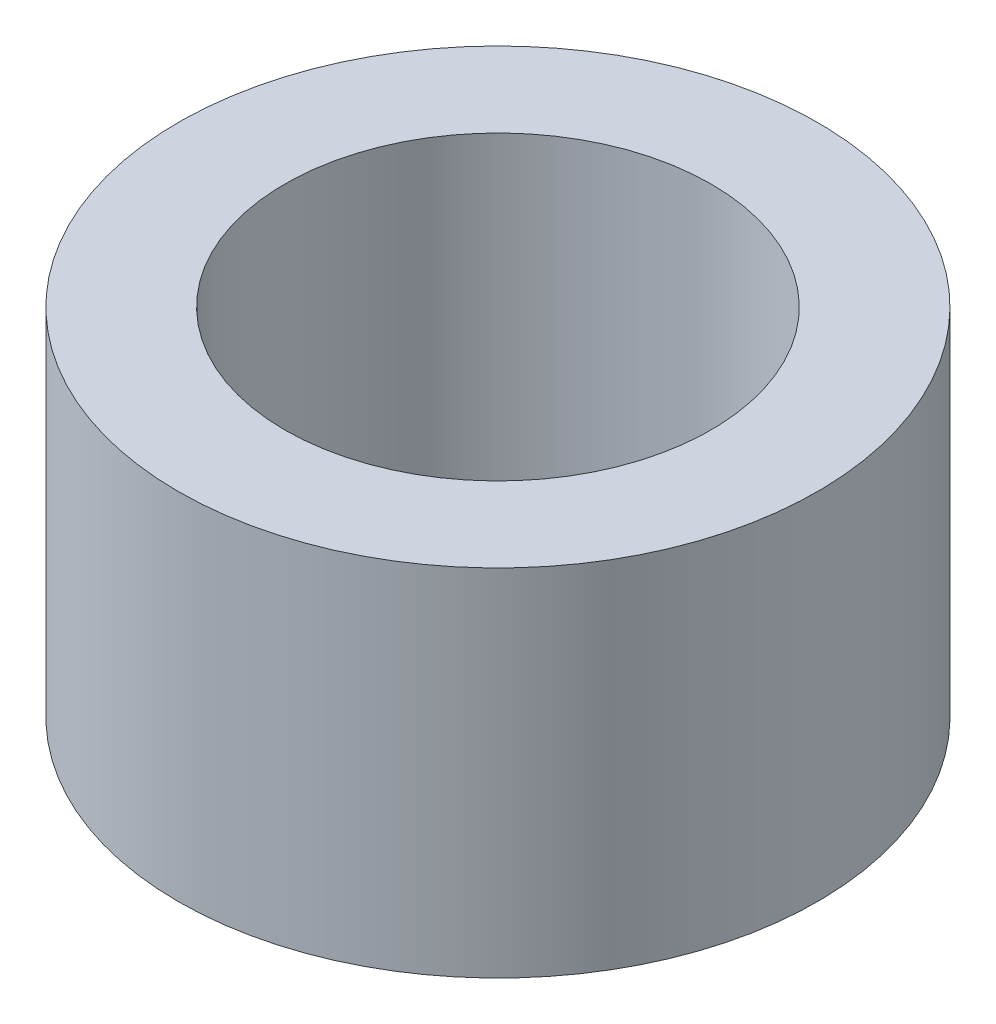
SolidWorks part; units mm, degrees
ref_plane "Front Plane" through (0, 0, 0) normal (0, 0, 1) x (1, 0, 0)
ref_plane "Top Plane" through (0, 0, 0) normal (0, 1, 0) x (1, 0, 0)
ref_plane "Right Plane" through (0, 0, 0) normal (1, 0, 0) x (0, 0, -1)
sketch "Sketch1" plane through (0, 0, 0) normal (0, 1, 0) x (1, 0, 0)
  circle A0 centre (0, 0) radius 9
extrude "Boss-Extrude1" add sketch "Sketch1" along normal blind 10
sketch "Sketch2" plane through (0, 10, 0) normal (0, 1, 0) x (1, 0, 0)
  circle A0 centre (0, 0) radius 6
extrude "Cut-Extrude1" cut sketch "Sketch2" against normal blind 10
